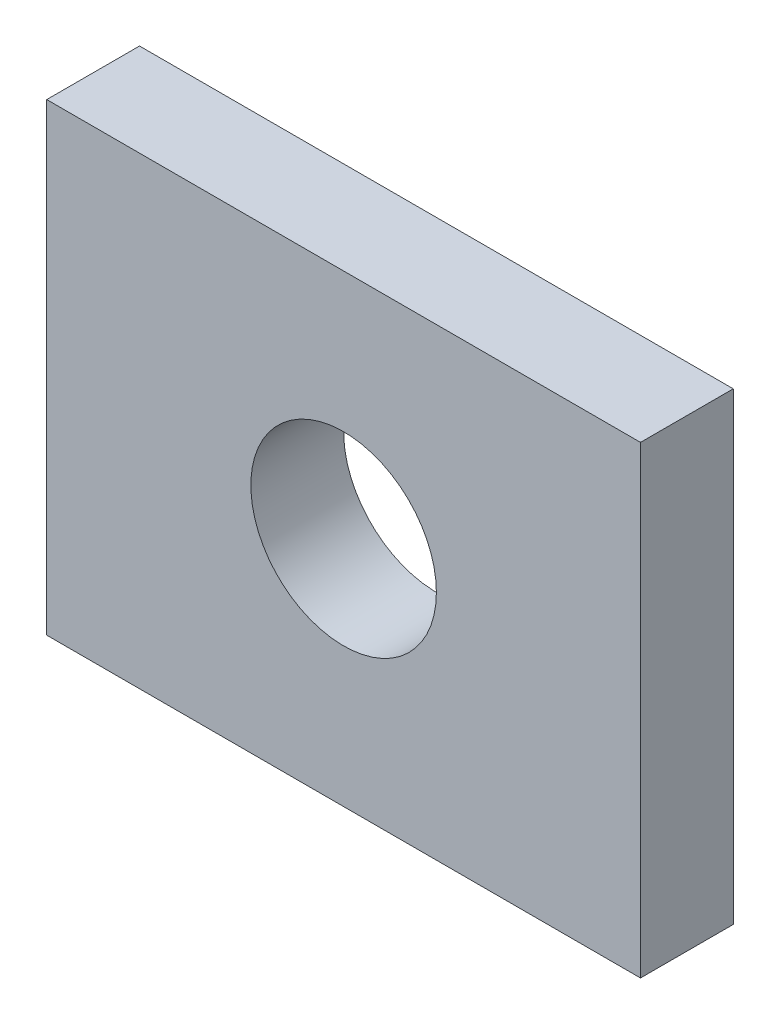
SolidWorks part; units mm, degrees
ref_plane "Alzado" through (0, 0, 0) normal (0, 0, 1) x (1, 0, 0)
ref_plane "Planta" through (0, 0, 0) normal (0, 1, 0) x (1, 0, 0)
ref_plane "Vista lateral" through (0, 0, 0) normal (1, 0, 0) x (0, 0, -1)
sketch "Croquis1" plane through (0, 0, 0) normal (0, 0, 1) x (1, 0, 0)
  line L1 (-16, -12.5) -> (16, -12.5)
  line L2 (-16, -12.5) -> (-16, 12.5)
  line L3 (-16, 12.5) -> (16, 12.5)
  line L4 (16, -12.5) -> (16, 12.5)
  line L5 (-16, -12.5) -> (16, 12.5) construction
  line L6 (-16, 12.5) -> (16, -12.5) construction
  circle A0 centre (0, 0) radius 5
  point P0 (0, 0)
  dimension "D1" = 32
  dimension "D2" = 25
extrude "Saliente-Extruir1" add sketch "Croquis1" along normal blind 5
